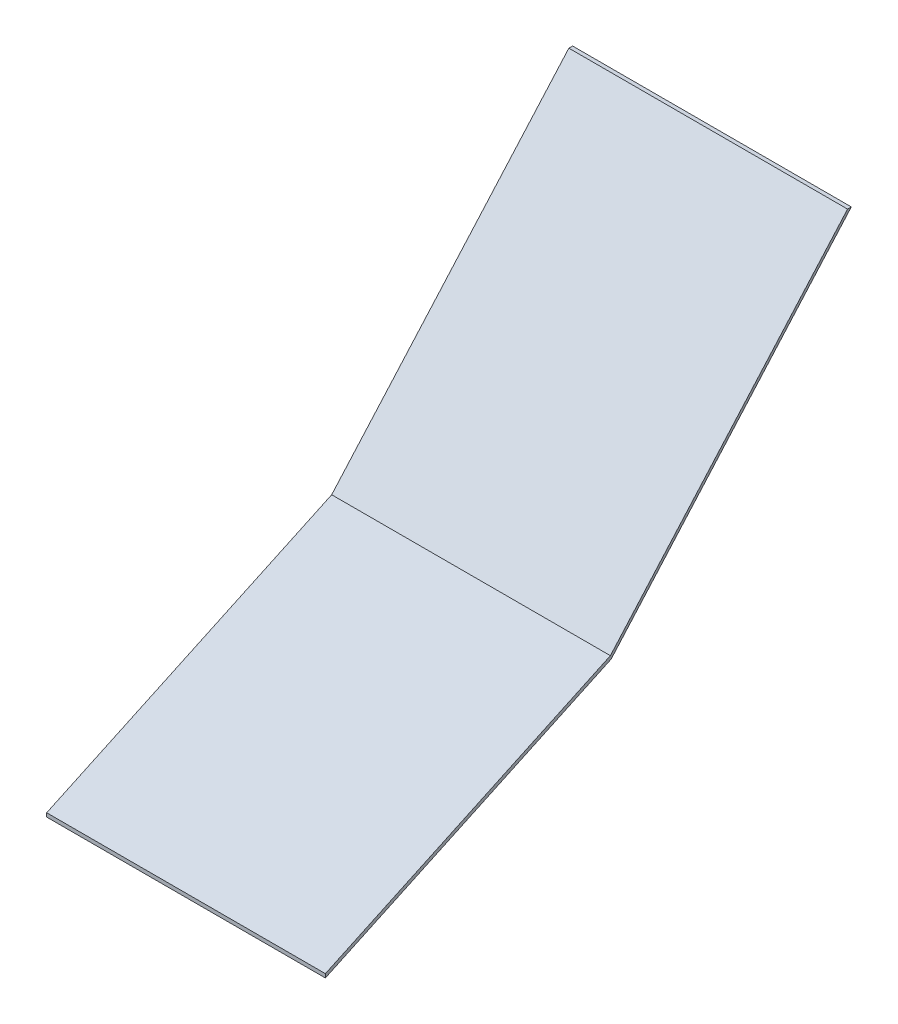
SolidWorks part; units mm, degrees
material "Plain Carbon Steel"
ref_plane "Front Plane" through (0, 0, 0) normal (0, 0, 1) x (1, 0, 0)
ref_plane "Top Plane" through (0, 0, 0) normal (0, 1, 0) x (1, 0, 0)
ref_plane "Right Plane" through (0, 0, 0) normal (1, 0, 0) x (0, 0, -1)
sketch "Sketch1" plane through (0, 0, 0) normal (1, 0, 0) x (0, 0, -1)
  line L0 (0, 0) -> (114.8023, 53.5332)
  line L1 (114.8023, 53.5332) -> (210.3387, 161.5555)
  line L2 (210.3387, 161.5555) -> (211.8577, 161.5555)
  line L3 (211.8577, 161.5555) -> (115.1011, 52.1536)
  line L4 (115.1011, 52.1536) -> (0, -1.5189)
  line L5 (0, -1.5189) -> (0, 0)
  line L6 (0, -1.5189) -> (0, -115.0076) construction
  point P3 (0, 0)
  point P9 (115.1011, 53.6861)
  point P10 (115.1011, 53.6622)
  dimension "D1" = 127
  dimension "D2" = 146.05
  dimension "D3" = 1.5189
  dimension "D4" = 1.5189
  dimension "D5" = 115
  dimension "D6" = 203.51
extrude "Boss-Extrude1" add sketch "Sketch1" along normal blind 112.268
